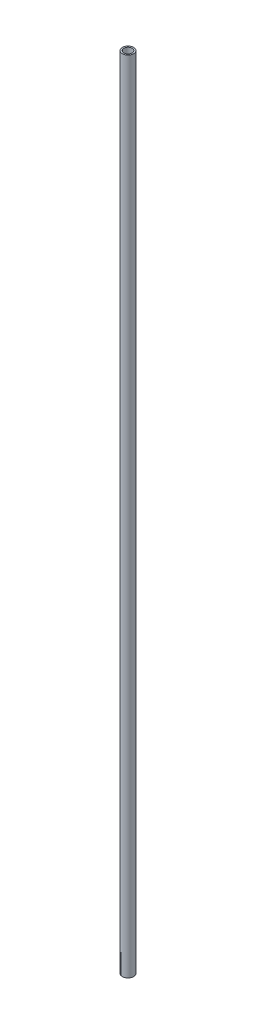
SolidWorks part; units mm, degrees
ref_plane "Front Plane" through (0, 0, 0) normal (0, 0, 1) x (1, 0, 0)
ref_plane "Top Plane" through (0, 0, 0) normal (0, 1, 0) x (1, 0, 0)
ref_plane "Right Plane" through (0, 0, 0) normal (1, 0, 0) x (0, 0, -1)
sketch "Sketch1" plane through (0, 0, 0) normal (0, 1, 0) x (1, 0, 0)
  circle A0 centre (0, 0) radius 7.8994
  circle A1 centre (0, 0) radius 10.668
  dimension "D1" = 15.7988
  dimension "D2" = 21.336
extrude "Boss-Extrude1" add sketch "Sketch1" along normal blind 1524
